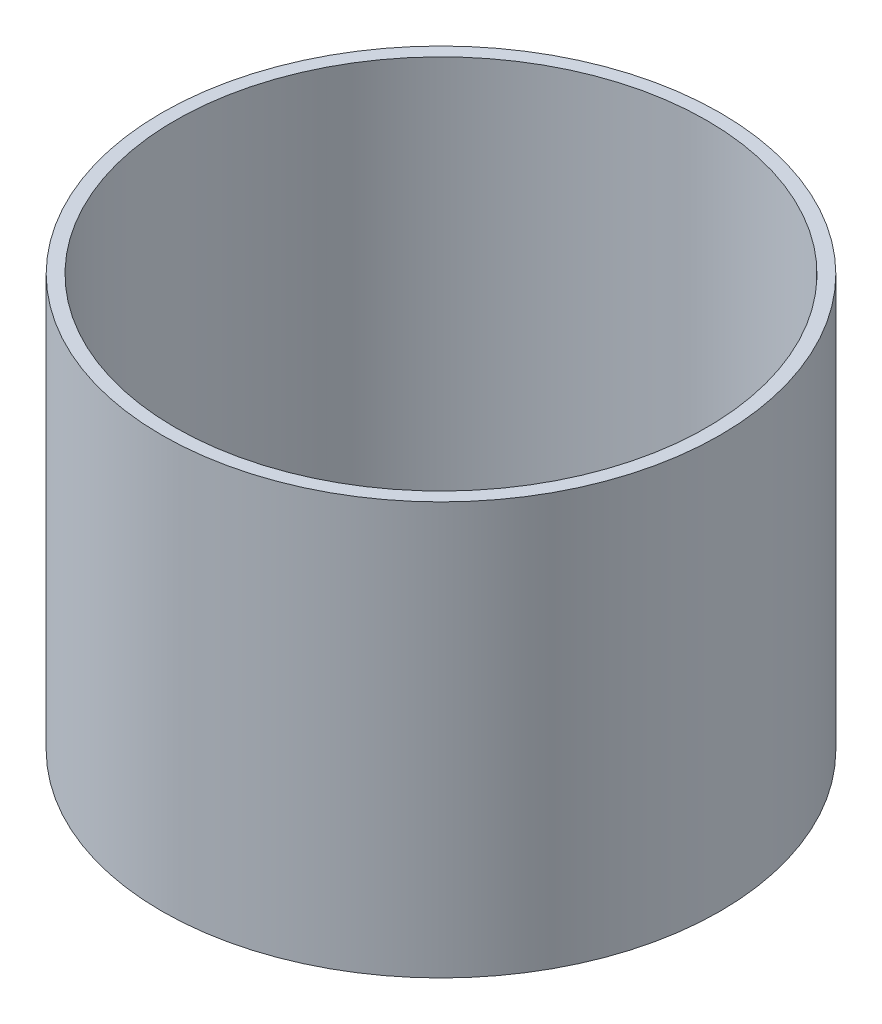
SolidWorks part; units mm, degrees
material "Corrugated Paper"
ref_plane "Front Plane" through (0, 0, 0) normal (0, 0, 1) x (1, 0, 0)
ref_plane "Top Plane" through (0, 0, 0) normal (0, 1, 0) x (1, 0, 0)
ref_plane "Right Plane" through (0, 0, 0) normal (1, 0, 0) x (0, 0, -1)
sketch "Sketch1" plane through (0, 0, 0) normal (0, 1, 0) x (1, 0, 0)
  circle A0 centre (0, 0) radius 93.345
  circle A1 centre (0, 0) radius 88.9
  dimension "D1" = 186.69
  dimension "D2" = 177.8
extrude "Boss-Extrude1" add sketch "Sketch1" along normal blind 137.8509
